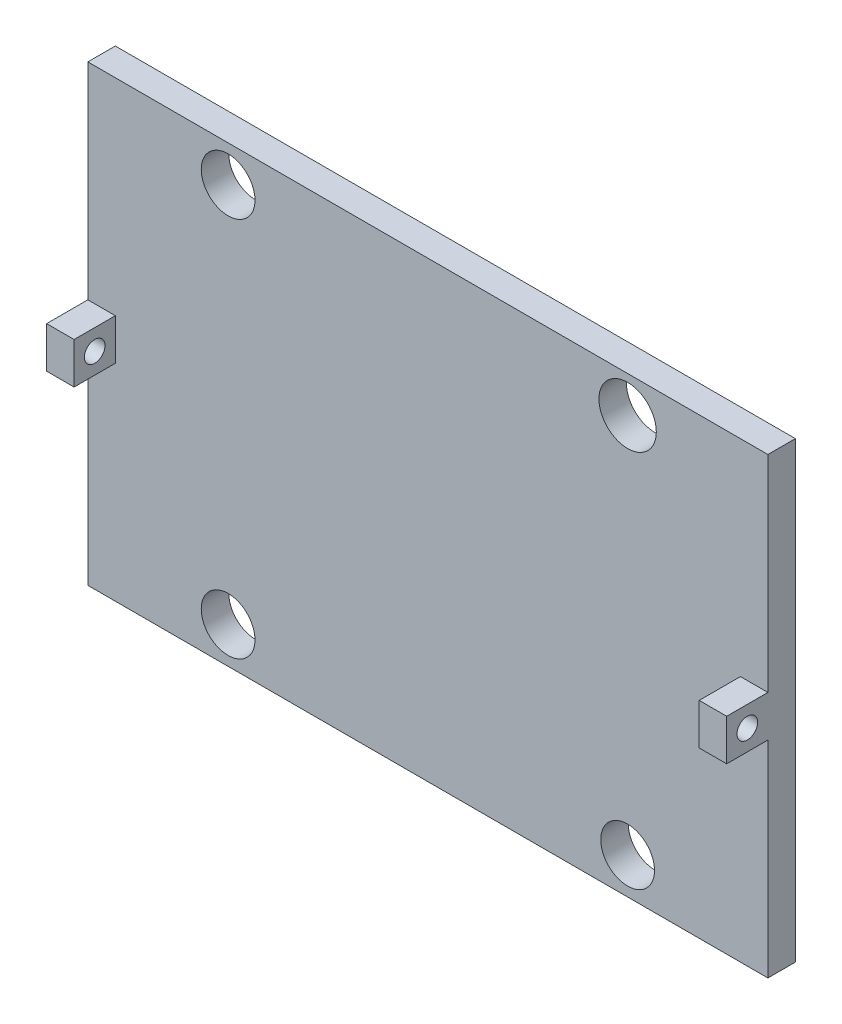
SolidWorks part; units mm, degrees
ref_plane "Front Plane" through (0, 0, 0) normal (0, 0, 1) x (1, 0, 0)
ref_plane "Top Plane" through (0, 0, 0) normal (0, 1, 0) x (1, 0, 0)
ref_plane "Right Plane" through (0, 0, 0) normal (1, 0, 0) x (0, 0, -1)
sketch "Sketch1" plane through (0, 0, 0) normal (0, 0, 1) x (1, 0, 0)
  line L1 (-31.7244, 10.1839) -> (17.7756, 10.1839)
  line L2 (-31.7244, 10.1839) -> (-31.7244, -22.8161)
  line L3 (-31.7244, -22.8161) -> (17.7756, -22.8161)
  line L4 (17.7756, 10.1839) -> (17.7756, -22.8161)
  dimension "D1" = 49.5
  dimension "D2" = 33
extrude "Boss-Extrude1" add sketch "Sketch1" along normal blind 2
sketch "Sketch8" plane through (0, 0, 2) normal (0, 0, 1) x (1, 0, 0)
  line L0 (-31.7244, -6.3161) -> (-31.7244, -4.8161)
  line L1 (-31.7244, 10.1839) -> (-31.7244, -22.8161) construction
  line L2 (-31.7244, -4.8161) -> (-29.7244, -4.8161)
  line L3 (-29.7244, -4.8161) -> (-29.7244, -7.8161)
  line L4 (-29.7244, -7.8161) -> (-31.7244, -7.8161)
  line L5 (-31.7244, -7.8161) -> (-31.7244, -6.3161)
  line L6 (17.7756, -4.8161) -> (17.7756, -7.8161)
  line L7 (15.7756, -4.8161) -> (17.7756, -4.8161)
  line L8 (17.7756, -7.8161) -> (15.7756, -7.8161)
  line L9 (15.7756, -7.8161) -> (15.7756, -6.3161)
  line L10 (15.7756, -6.3161) -> (15.7756, -4.8161)
  dimension "D1" = 2
extrude "Boss-Extrude4" add sketch "Sketch8" along normal blind 3
sketch "Sketch9" plane through (-31.7244, 0, 0) normal (-1, 0, 0) x (0, 0, 1)
  circle A0 centre (3.5, -6.3161) radius 0.75
extrude "Cut-Extrude3" cut sketch "Sketch9" against normal blind 70
sketch "Sketch10" plane through (0, 0, 0) normal (0, 0, -1) x (-1, 0, 0)
  line L8 (-7.5656, -20.1718) -> (21.5144, 7.5396) construction
  line L9 (-7.5656, 7.5396) -> (21.5144, -20.1718) construction
  circle A0 centre (-7.5656, 7.5396) radius 2.087
  circle A1 centre (21.5144, 7.5396) radius 1.9558
  circle A2 centre (-7.5656, -20.1718) radius 1.9558
  circle A3 centre (21.5144, -20.1718) radius 1.9558
  point P6 (6.9744, -6.3161)
  dimension "D1" = 29.08
  dimension "D2" = 27.7114
extrude "Cut-Extrude4" cut sketch "Sketch10" against normal blind 70
